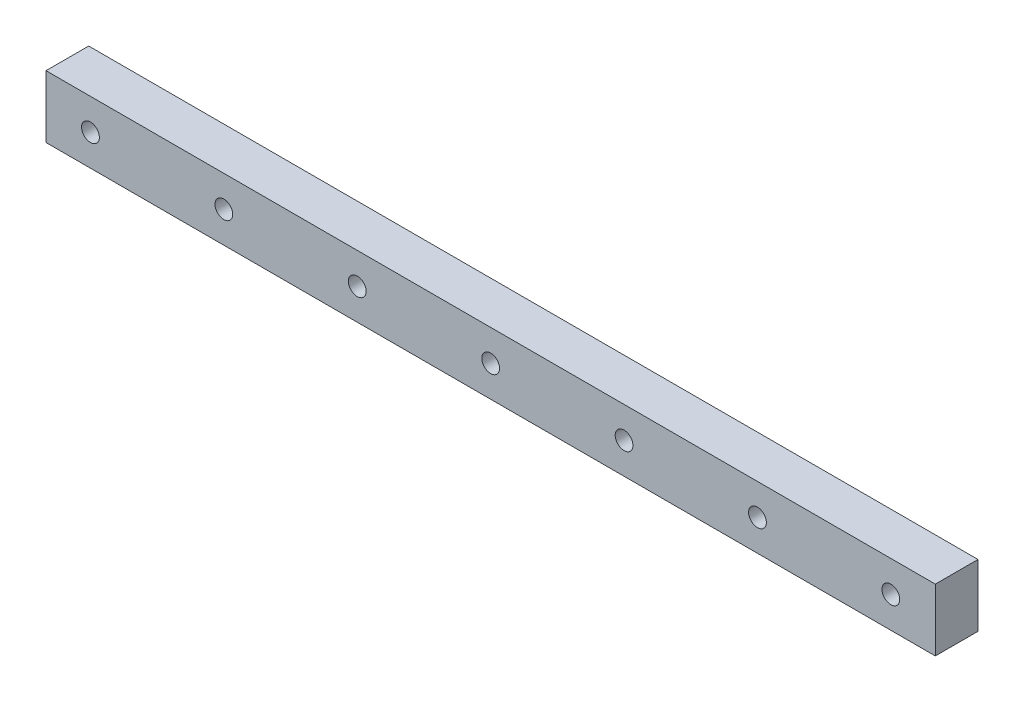
SolidWorks part; units mm, degrees
ref_plane "Front" through (0, 0, 0) normal (0, 0, 1) x (1, 0, 0)
ref_plane "Top" through (0, 0, 0) normal (0, 1, 0) x (1, 0, 0)
ref_plane "Right" through (0, 0, 0) normal (1, 0, 0) x (0, 0, -1)
sketch "草图1" plane through (0, 0, 0) normal (0, 0, 1) x (1, 0, 0)
  line L9 (0, 0) -> (100, 0)
  line L10 (0, 0) -> (0, 7)
  line L11 (0, 7) -> (100, 7)
  line L12 (100, 0) -> (100, 7)
  circle A10 centre (5, 3.5) radius 1
  circle A11 centre (20, 3.5) radius 1
  circle A12 centre (35, 3.5) radius 1
  circle A13 centre (50, 3.5) radius 1
  circle A14 centre (65, 3.5) radius 1
  circle A15 centre (80, 3.5) radius 1
  circle A16 centre (95, 3.5) radius 1
  dimension "D1" = 5
  dimension "D2" = 3.5
  dimension "D3" = 7
extrude "凸台-拉伸1" add sketch "草图1" along normal blind 4.8
